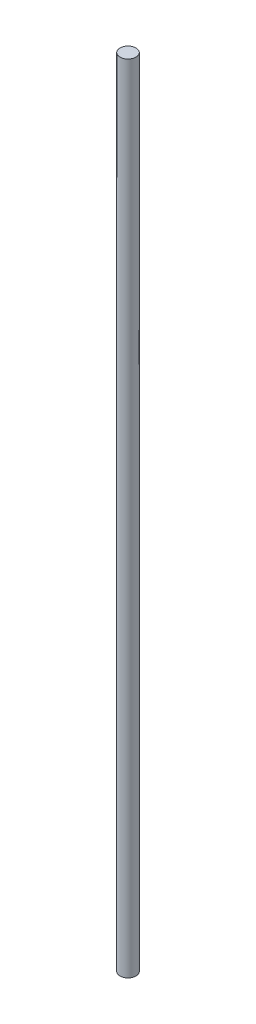
SolidWorks part; units mm, degrees
ref_plane "Front Plane" through (0, 0, 0) normal (0, 0, 1) x (1, 0, 0)
ref_plane "Top Plane" through (0, 0, 0) normal (0, 1, 0) x (1, 0, 0)
ref_plane "Right Plane" through (0, 0, 0) normal (1, 0, 0) x (0, 0, -1)
sketch "Sketch1" plane through (0, 0, 0) normal (0, 1, 0) x (1, 0, 0)
  circle A0 centre (0, 0) radius 2.54
  dimension "D1" = 5.08
extrude "Boss-Extrude1" add sketch "Sketch1" along normal blind 253.238
